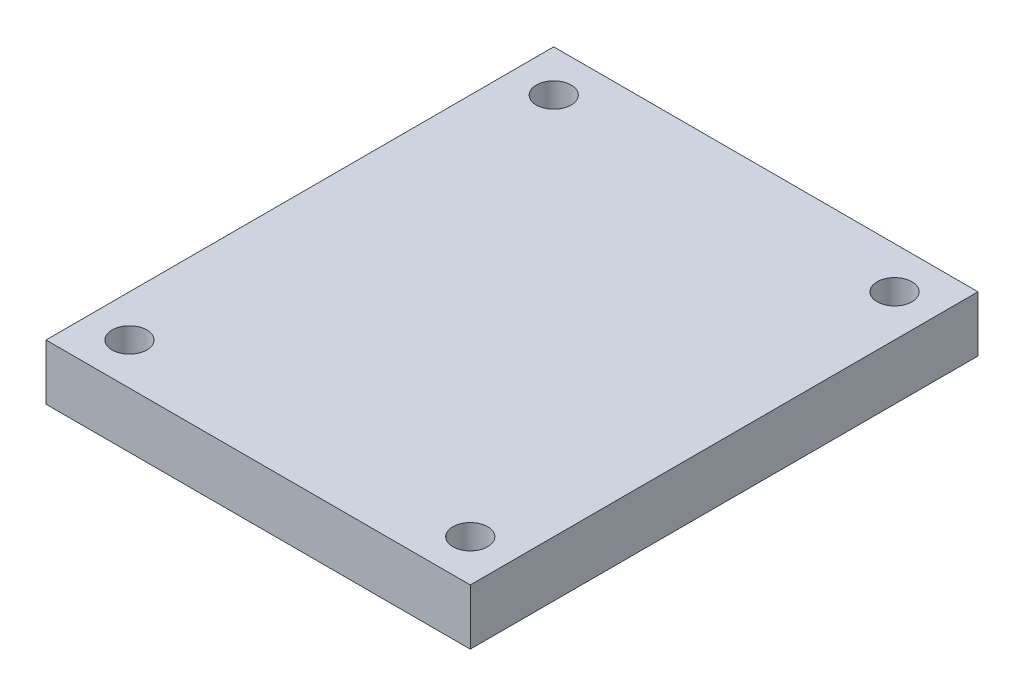
SolidWorks part; units mm, degrees
material "1060 Alloy"
ref_plane "Front Plane" through (0, 0, 0) normal (0, 0, 1) x (1, 0, 0)
ref_plane "Top Plane" through (0, 0, 0) normal (0, 1, 0) x (1, 0, 0)
ref_plane "Right Plane" through (0, 0, 0) normal (1, 0, 0) x (0, 0, -1)
sketch "Sketch1" plane through (0, 0, 0) normal (0, 1, 0) x (1, 0, 0)
  line L1 (-12.25, 12.25) -> (12.25, 12.25)
  line L2 (-12.25, 12.25) -> (-12.25, -12.25)
  line L3 (-12.25, -12.25) -> (12.25, -12.25)
  line L4 (12.25, 12.25) -> (12.25, -12.25)
  line L5 (-12.25, 12.25) -> (12.25, -12.25) construction
  line L6 (-12.25, -12.25) -> (12.25, 12.25) construction
  point P0 (0, 0)
  dimension "D1" = 24.5
  dimension "D2" = 24.5
extrude "Boss-Extrude1" add sketch "Sketch1" along normal mid plane 4
sketch "Sketch2" plane through (0, 2, 0) normal (0, 1, 0) x (1, 0, 0)
  line L1 (12.25, -12.25) -> (-12.25, -12.25)
  line L2 (12.25, -12.25) -> (12.25, 12.25)
  line L3 (12.25, 12.25) -> (-12.25, 12.25)
  line L4 (-12.25, -12.25) -> (-12.25, 12.25)
  line L7 (-15.25, 18.25) -> (15.25, 18.25)
  line L8 (-15.25, 18.25) -> (-15.25, -18.25)
  line L9 (-15.25, -18.25) -> (15.25, -18.25)
  line L10 (15.25, 18.25) -> (15.25, -18.25)
  point P0 (0, 0)
  dimension "D1" = 6
  dimension "D2" = 6
  dimension "D3" = 3
  dimension "D4" = 3
  dimension "D5" = 24.5
extrude "Boss-Extrude2" add sketch "Sketch2" against normal blind 4
sketch "Sketch3" plane through (0, 2, 0) normal (0, 1, 0) x (1, 0, 0)
  line L0 (15.25, 18.25) -> (-15.25, 18.25) construction
  line L1 (-15.25, 18.25) -> (-15.25, -18.25) construction
  line L2 (15.25, -18.25) -> (15.25, 18.25) construction
  line L3 (-15.25, -18.25) -> (15.25, -18.25) construction
  point P0 (-12.25, 15.25)
  point P1 (12.25, 15.25)
  point P2 (-12.25, -15.25)
  point P3 (12.25, -15.25)
  dimension "D1" = 3
  dimension "D2" = 3
  dimension "D3" = 3
  dimension "D4" = 3
  dimension "D5" = 3
  dimension "D6" = 3
  dimension "D7" = 3
  dimension "D8" = 3
hole_wizard "M3x0.5 Tapped Hole1" positions "Sketch4" profile "Sketch5" tap size "M3x0.5" standard "ANSI Metric" end condition through all
sketch "Sketch4" plane through (0, 2, 0) normal (0, 1, 0) x (1, 0, 0)
  point P0 (-12.25, 15.25)
  point P3 (12.25, 15.25)
  point P6 (-12.25, -15.25)
  point P9 (12.25, -15.25)
sketch "Sketch5" plane through (-12.25, 2, -15.25) normal (1, 0, 0) x (0, 0, 1)
  line L0 (0, 0) -> (0, 4)
  line L1 (0, 4) -> (1.25, 4)
  line L2 (1.25, 4) -> (1.25, 0)
  line L5 (1.25, 0) -> (0, 0)
  line L11 (0, -6.35) -> (0, 107.95) construction
  dimension "Thru Tap Drill Dia." = 2.5
  dimension "Thru Tap Drill Depth" = 4
cosmetic thread "Hole Thread1" parameters "D2"=3
cosmetic thread "Hole Thread2" parameters "D2"=3
cosmetic thread "Hole Thread3" parameters "D2"=3
cosmetic thread "Hole Thread4" parameters "D2"=3
